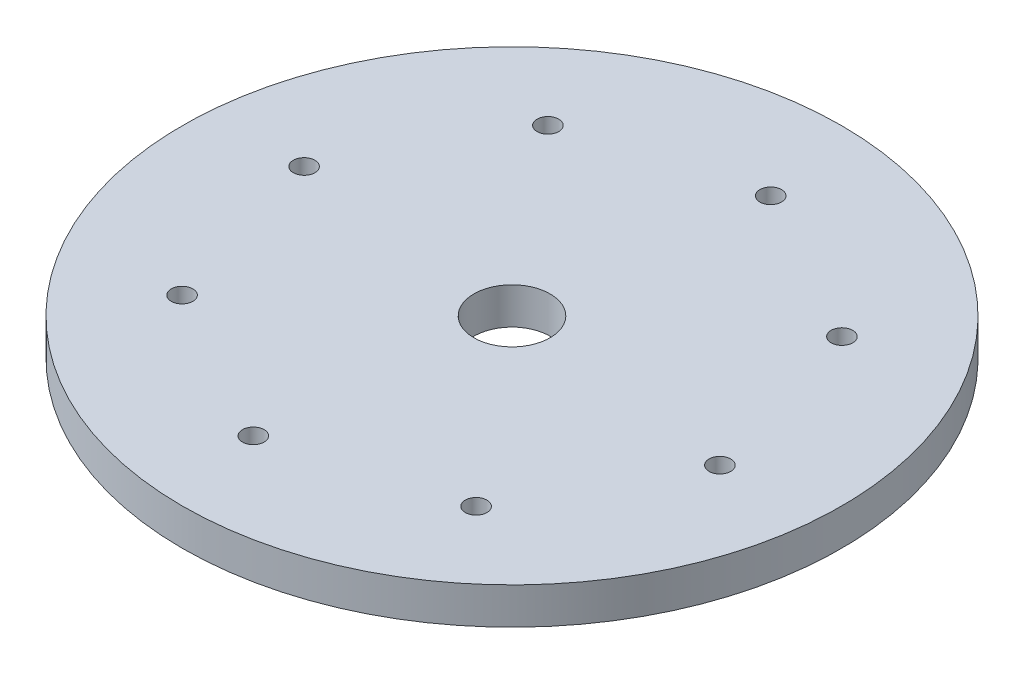
SolidWorks part; units mm, degrees
ref_plane "Front Plane" through (0, 0, 0) normal (0, 0, 1) x (1, 0, 0)
ref_plane "Top Plane" through (0, 0, 0) normal (0, 1, 0) x (1, 0, 0)
ref_plane "Right Plane" through (0, 0, 0) normal (1, 0, 0) x (0, 0, -1)
sketch "Sketch1" plane through (0, 0, 0) normal (0, 1, 0) x (1, 0, 0)
  circle A0 centre (0, 0) radius 53.5432
  circle A1 centre (0, 0) radius 6.1849
  circle A2 centre (37.9031, -4.1253) radius 1.759
  circle A3 centre (0, 0) radius 38.127 construction
  circle A4 centre (23.8845, -29.7186) radius 1.7589
  circle A5 centre (0, 0) radius 38.127 construction
  circle A6 centre (-4.1253, -37.9031) radius 1.759
  circle A7 centre (0, 0) radius 38.127 construction
  circle A8 centre (-29.7186, -23.8845) radius 1.7589
  circle A9 centre (0, 0) radius 38.127 construction
  circle A10 centre (-37.9031, 4.1253) radius 1.759
  circle A11 centre (0, 0) radius 38.127 construction
  circle A12 centre (-23.8845, 29.7186) radius 1.7589
  circle A13 centre (0, 0) radius 38.127 construction
  circle A14 centre (4.1253, 37.9031) radius 1.759
  circle A15 centre (0, 0) radius 38.127 construction
  circle A16 centre (29.7186, 23.8845) radius 1.759
  circle A17 centre (0, 0) radius 38.127 construction
  point P7 (39.6621, -4.1253)
  point P8 (-6.1849, 0)
  point P32 (0, 0)
  dimension "D1" = 107.0864
  dimension "D2" = 12.3698
  dimension "D3" = 3.5179
  dimension "D4" = 45.847
  dimension "D5" = 8
extrude "Boss-Extrude1" add sketch "Sketch1" along normal blind 5.9563
